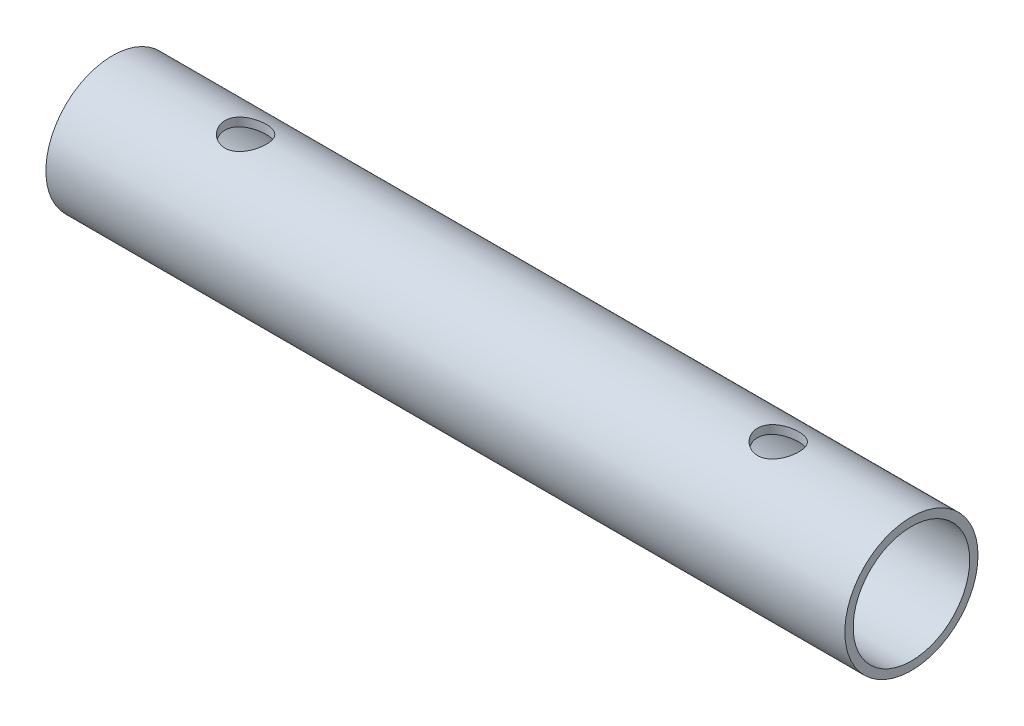
SolidWorks part; units mm, degrees
material "AISI 304"
ref_plane "Front" through (0, 0, 0) normal (0, 0, 1) x (1, 0, 0)
ref_plane "Top" through (0, 0, 0) normal (0, 1, 0) x (1, 0, 0)
ref_plane "Right" through (0, 0, 0) normal (1, 0, 0) x (0, 0, -1)
sketch "草图1" plane through (0, 0, 0) normal (1, 0, 0) x (0, 0, -1)
  circle A0 centre (0, 0) radius 8.75
  circle A1 centre (0, 0) radius 10
extrude "凸台-拉伸1" add sketch "草图1" along normal blind 120
sketch "草图2" plane through (0, 0, 0) normal (0, 1, 0) x (1, 0, 0)
  line L0 (0, 0) -> (20, 0) construction
  line L1 (0, 0) -> (100, 0) construction
  circle A0 centre (20, 0) radius 3.1
  circle A1 centre (100, 0) radius 3.1
extrude "切除-拉伸1" cut sketch "草图2" against normal through all both and the other way through all
